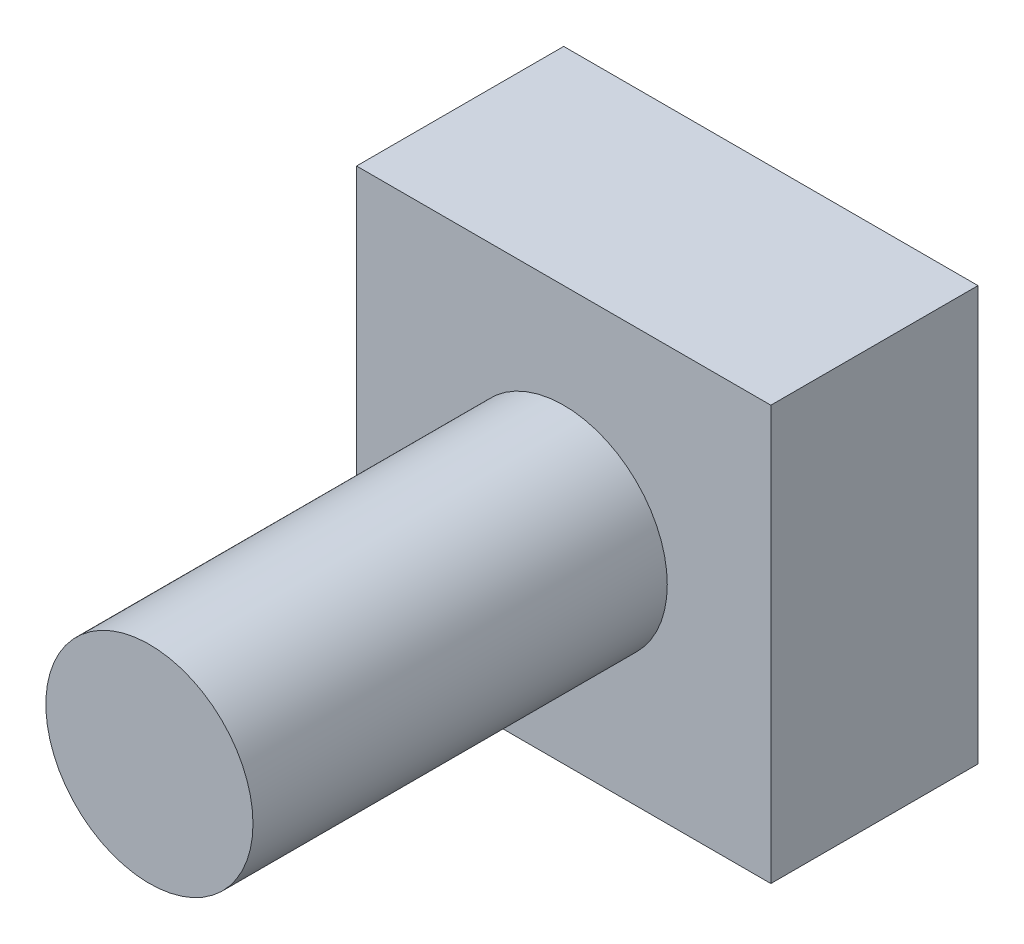
SolidWorks part; units mm, degrees
ref_plane "Front" through (0, 0, 0) normal (0, 0, 1) x (1, 0, 0)
ref_plane "Top" through (0, 0, 0) normal (0, 1, 0) x (1, 0, 0)
ref_plane "Right" through (0, 0, 0) normal (1, 0, 0) x (0, 0, -1)
sketch "Sketch2" plane through (0, 0, 0) normal (0, 0, 1) x (1, 0, 0)
  line L0 (6.35, 12.7) -> (6.35, 0) construction
  line L1 (0, 0) -> (12.7, 0)
  line L2 (0, 0) -> (0, 12.7)
  line L3 (0, 12.7) -> (12.7, 12.7)
  line L4 (12.7, 0) -> (12.7, 12.7)
  dimension "D1" = 12.7
  dimension "D2" = 12.7
extrude "Boss-Extrude1" add sketch "Sketch2" along normal blind 6.35 contours L2 L3 L4 L1
sketch "Sketch3" plane through (0, 0, 6.35) normal (0, 0, 1) x (1, 0, 0)
  line L0 (6.35, 12.7) -> (6.35, 0) construction
  line L1 (0, 12.7) -> (12.7, 12.7) construction
  line L2 (0, 0) -> (12.7, 0) construction
  circle A0 centre (6.35, 6.35) radius 3.175
extrude "Boss-Extrude2" add sketch "Sketch3" along normal blind 12.7
